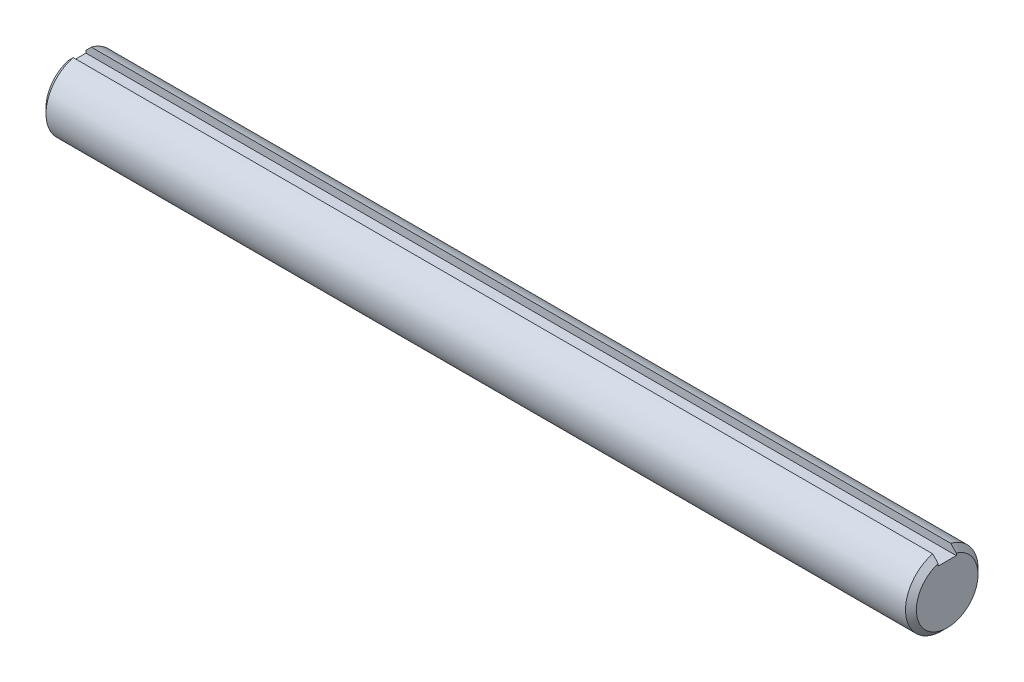
SolidWorks part; units mm, degrees
material "AISI 1045 Steel, cold drawn"
ref_plane "Front" through (0, 0, 0) normal (0, 0, 1) x (1, 0, 0)
ref_plane "Top" through (0, 0, 0) normal (0, 1, 0) x (1, 0, 0)
ref_plane "Right" through (0, 0, 0) normal (1, 0, 0) x (0, 0, -1)
sketch "Sketch1" plane through (0, 0, 0) normal (1, 0, 0) x (0, 0, -1)
  circle A0 centre (0, 0) radius 12.7
  dimension "dia" = 25.4
extrude "Extrude1" add sketch "Sketch1" along normal mid plane 304.8
sketch "Sketch2" plane through (0, 0, 0) normal (0, 0, 1) x (1, 0, 0)
  point P0 (152.4, 12.7)
  point P1 (-152.4, 12.7)
  point P2 (-152.4, -12.7)
chamfer "Chamfer1" distance 1.905 angle 45 2 edges at (-152.4, 0, -12.7) (152.4, 0, -12.7)
sketch "Sketch3" plane through (0, 0, 0) normal (1, 0, 0) x (0, 0, -1)
  line L1 (-3.175, 12.7) -> (3.175, 12.7)
  line L2 (-3.175, 12.7) -> (-3.175, 9.525)
  line L3 (-3.175, 9.525) -> (3.175, 9.525)
  line L4 (3.175, 12.7) -> (3.175, 9.525)
  dimension "key wd" = 6.35
  dimension "key dp" = 3.175
extrude "Extrude2" cut sketch "Sketch3" against normal through all and the other way through all
equation "\"D1@Chamfer1\" = \"dia@Sketch1\" * .075"
